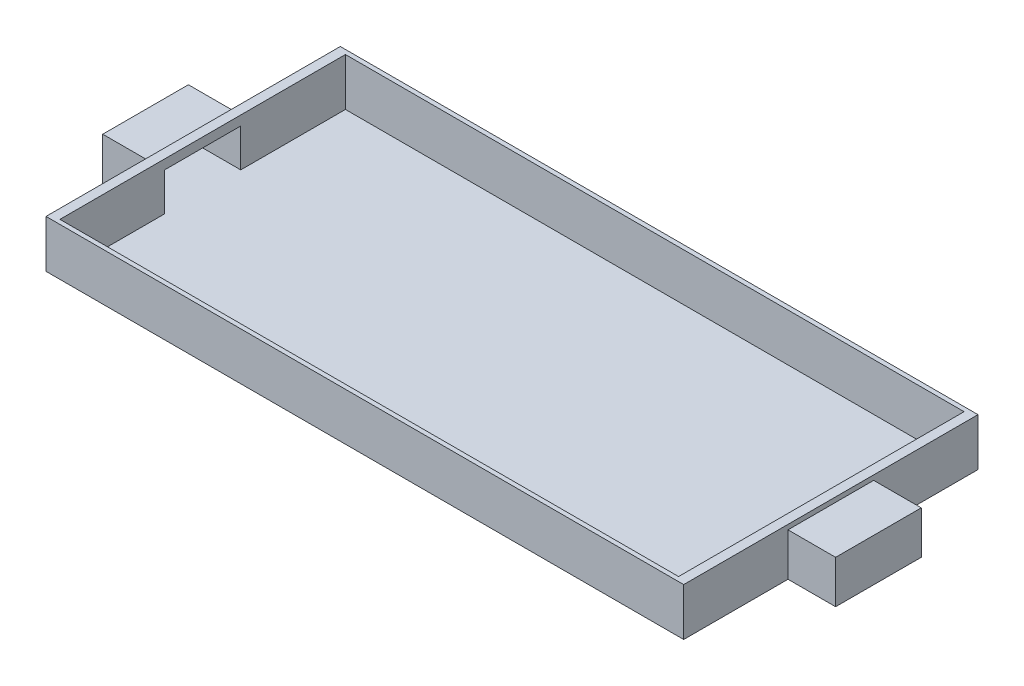
SolidWorks part; units mm, degrees
ref_plane "前基準面" through (0, 0, 0) normal (0, 0, 1) x (1, 0, 0)
ref_plane "上基準面" through (0, 0, 0) normal (0, 1, 0) x (1, 0, 0)
ref_plane "右基準面" through (0, 0, 0) normal (1, 0, 0) x (0, 0, -1)
sketch "草圖1" plane through (0, 0, 0) normal (0, 1, 0) x (1, 0, 0)
  line L1 (-3.35, 1.5462) -> (3.35, 1.5462)
  line L2 (-3.35, 1.5462) -> (-3.35, -1.5462)
  line L3 (-3.35, -1.5462) -> (3.35, -1.5462)
  line L4 (3.35, 1.5462) -> (3.35, -1.5462)
  line L5 (-3.35, 1.5462) -> (3.35, -1.5462) construction
  line L6 (-3.35, -1.5462) -> (3.35, 1.5462) construction
  line L7 (-3.25, 1.5) -> (3.25, 1.5)
  line L8 (-3.25, 1.5) -> (-3.25, -1.5)
  line L9 (-3.25, -1.5) -> (3.25, -1.5)
  line L10 (3.25, 1.5) -> (3.25, -1.5)
  line L11 (-3.25, 1.5) -> (3.25, -1.5) construction
  line L12 (-3.25, -1.5) -> (3.25, 1.5) construction
  point P0 (0, 0)
  point P6 (0, 0)
  point P11 (0, 0)
  point P12 (0, 0)
  dimension "D1" = 6.5
  dimension "D2" = 3
  dimension "D3" = 0.1
extrude "填料-伸長1" add sketch "草圖1" along normal blind 0.5
sketch "草圖3" plane through (-3.35, 0, 0) normal (-1, 0, 0) x (0, 0, 1)
  line L0 (-1.5462, 0) -> (1.5462, 0) construction
  line L1 (-0.4, 0.4) -> (0.4, 0.4)
  line L2 (-0.4, 0.4) -> (-0.4, 0)
  line L3 (-0.4, 0) -> (0.4, 0)
  line L4 (0.4, 0.4) -> (0.4, 0)
  line L5 (-0.4, 0.4) -> (0.4, 0) construction
  line L6 (-0.4, 0) -> (0.4, 0.4) construction
  point P0 (0, 0.2)
  point P5 (0, 0)
  point P9 (0, 0)
  point P10 (0, 0)
  dimension "D1" = 0.4
  dimension "D2" = 0.8
extrude "除料-伸長1" cut sketch "草圖3" along normal through all and the other way through all
sketch "草圖8" plane through (-3.35, 0, 0) normal (-1, 0, 0) x (0, 0, 1)
  line L0 (-0.45, 0) -> (-0.45, 0.45)
  line L1 (-1.5462, 0) -> (-0.4, 0) construction
  line L2 (-0.45, 0.45) -> (0.45, 0.45)
  line L3 (0.45, 0.45) -> (0.45, 0)
  line L4 (0.4, 0) -> (1.5462, 0) construction
  line L5 (0.45, 0) -> (-0.45, 0)
  dimension "D1" = 0.05
  dimension "D2" = 0.05
  dimension "D3" = 0.05
extrude "填料-伸長4" add sketch "草圖8" along normal blind 0.5
sketch "草圖9" plane through (-3.35, 0, 0) normal (1, 0, 0) x (0, 0, -1)
  line L4 (-0.4, 0.4) -> (-0.4, 0)
  line L5 (-0.4, 0) -> (0.4, 0)
  line L6 (0.4, 0) -> (0.4, 0.4)
  line L7 (0.4, 0.4) -> (-0.4, 0.4)
  line L8 (-0.4, 0.4) -> (-0.4, 0)
  line L9 (-0.4, 0) -> (0.4, 0)
  line L10 (0.4, 0) -> (0.4, 0.4)
  line L11 (0.4, 0.4) -> (-0.4, 0.4)
  dimension "D1" = 0
extrude "除料-伸長2" cut sketch "草圖9" against normal blind 0.45
mirror "鏡射7" about plane through (0, 0, 0) normal (1, 0, 0) of "除料-伸長2", "填料-伸長4"
surface "曲面-平面2"
